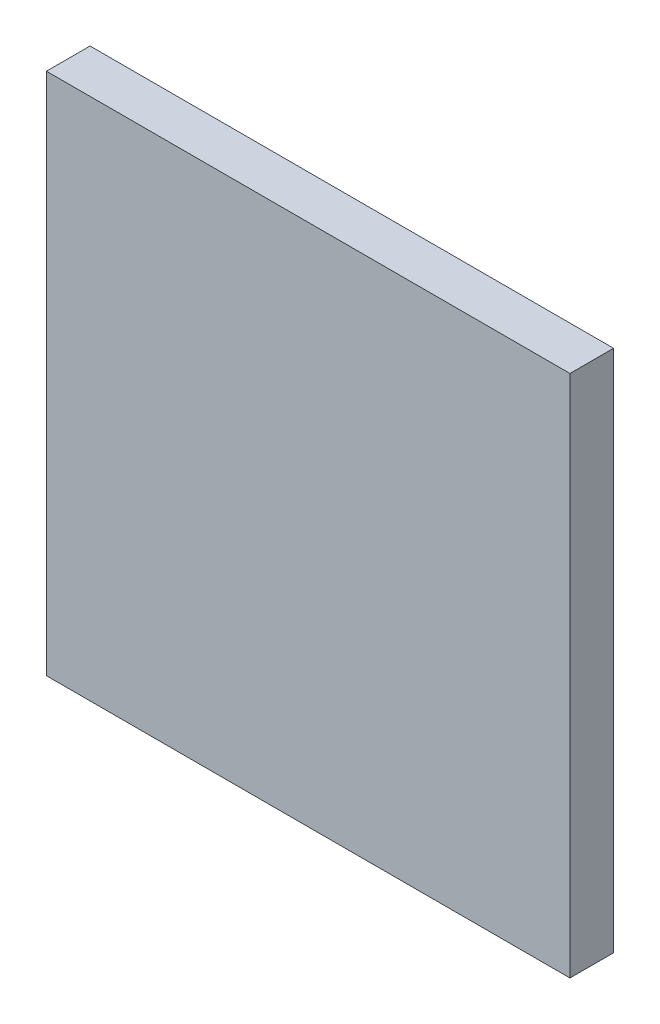
SolidWorks part; units mm, degrees
ref_plane "Front Plane" through (0, 0, 0) normal (0, 0, 1) x (1, 0, 0)
ref_plane "Top Plane" through (0, 0, 0) normal (0, 1, 0) x (1, 0, 0)
ref_plane "Right Plane" through (0, 0, 0) normal (1, 0, 0) x (0, 0, -1)
sketch "Sketch1" plane through (0, 0, 0) normal (0, 0, 1) x (1, 0, 0)
  line L1 (0, 0) -> (76.2, 0)
  line L2 (0, 0) -> (0, 76.2)
  line L3 (0, 76.2) -> (76.2, 76.2)
  line L4 (76.2, 0) -> (76.2, 76.2)
  dimension "D1" = 76.2
  dimension "D2" = 76.2
extrude "Boss-Extrude1" add sketch "Sketch1" along normal blind 6.35
